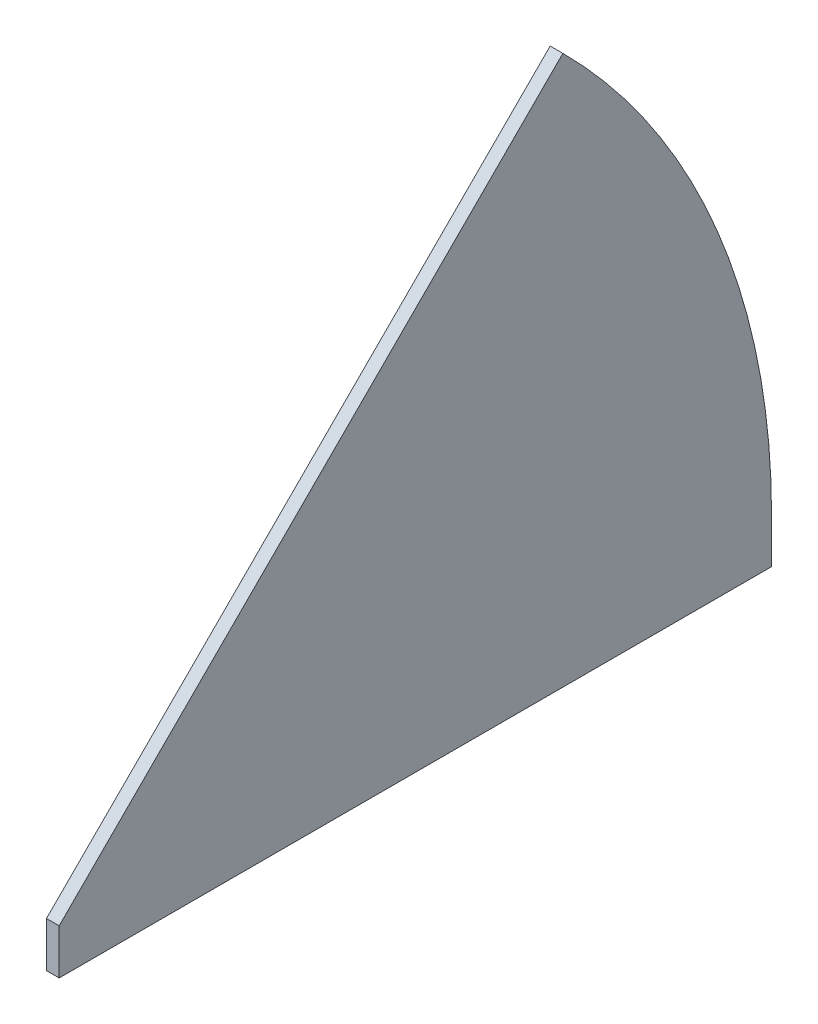
SolidWorks part; units mm, degrees
ref_plane "Front" through (0, 0, 0) normal (0, 0, 1) x (1, 0, 0)
ref_plane "Top" through (0, 0, 0) normal (0, 1, 0) x (1, 0, 0)
ref_plane "Right" through (0, 0, 0) normal (1, 0, 0) x (0, 0, -1)
sketch "Sketch1" plane through (0, 0, 0) normal (1, 0, 0) x (0, 0, -1)
  line L0 (0, 0) -> (178.054, 0)
  line L1 (0, 0) -> (125.9032, 125.9032)
  arc A0 (178.054, 0) -> (125.9032, 125.9032) centre (0, 0) ccw
  dimension "D1" = 356.108
  dimension "D2" = 45
extrude "Boss-Extrude1" add sketch "Sketch1" along normal blind 3.175
sketch "Sketch2" plane through (0, 0, 0) normal (0, -1, 0) x (1, 0, 0)
  line L1 (0, -178.054) -> (3.175, -178.054)
  line L2 (0, -178.054) -> (0, 0)
  line L3 (0, 0) -> (3.175, 0)
  line L4 (3.175, -178.054) -> (3.175, 0)
extrude "Boss-Extrude2" add sketch "Sketch2" along normal blind 11.303
